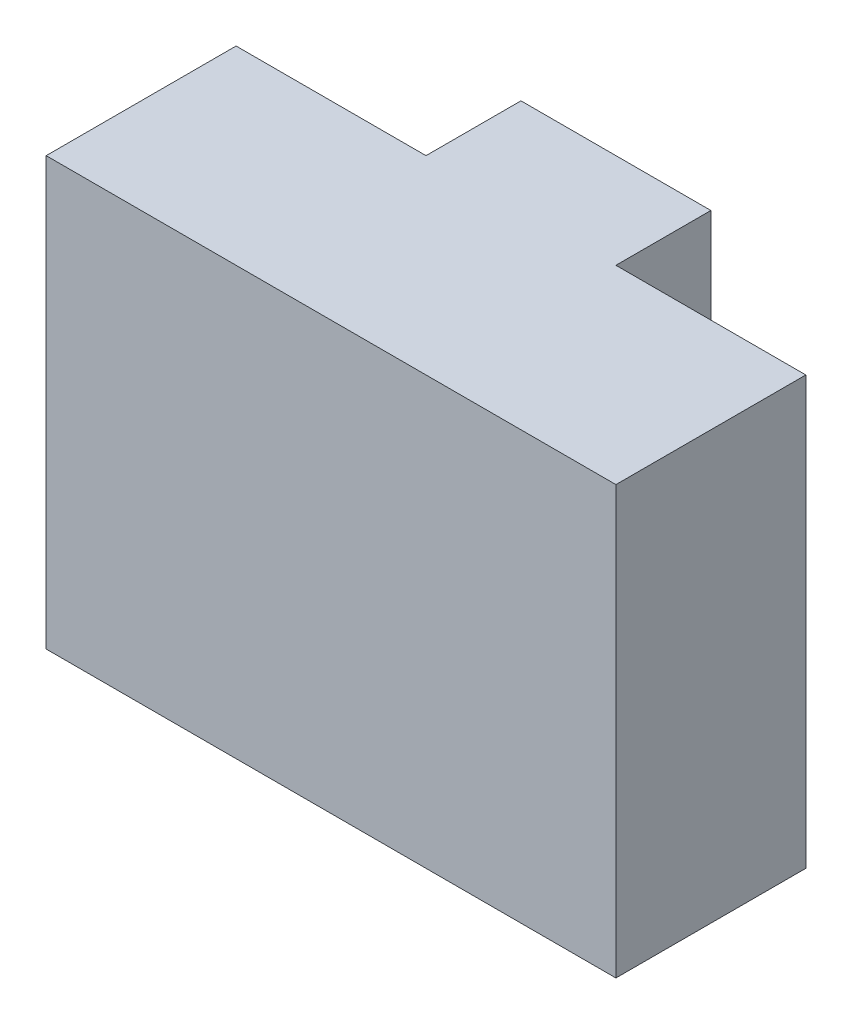
SolidWorks part; units mm, degrees
ref_plane "Front Plane" through (0, 0, 0) normal (0, 0, 1) x (1, 0, 0)
ref_plane "Top Plane" through (0, 0, 0) normal (0, 1, 0) x (1, 0, 0)
ref_plane "Right Plane" through (0, 0, 0) normal (1, 0, 0) x (0, 0, -1)
sketch "Sketch1" plane through (0, 0, 0) normal (0, 1, 0) x (1, 0, 0)
  line L0 (-30, 0) -> (30, 0)
  line L1 (30, 0) -> (30, 20)
  line L2 (30, 20) -> (10, 20)
  line L3 (10, 20) -> (10, 30)
  line L4 (10, 30) -> (-10, 30)
  line L5 (-10, 30) -> (-10, 20)
  line L6 (-10, 20) -> (-30, 20)
  line L7 (-30, 20) -> (-30, 0)
  point P3 (0, 0)
  dimension "D1" = 20
  dimension "D2" = 60
  dimension "D3" = 20
  dimension "D4" = 30
  dimension "D5" = 20
extrude "Boss-Extrude1" add sketch "Sketch1" along normal blind 45
